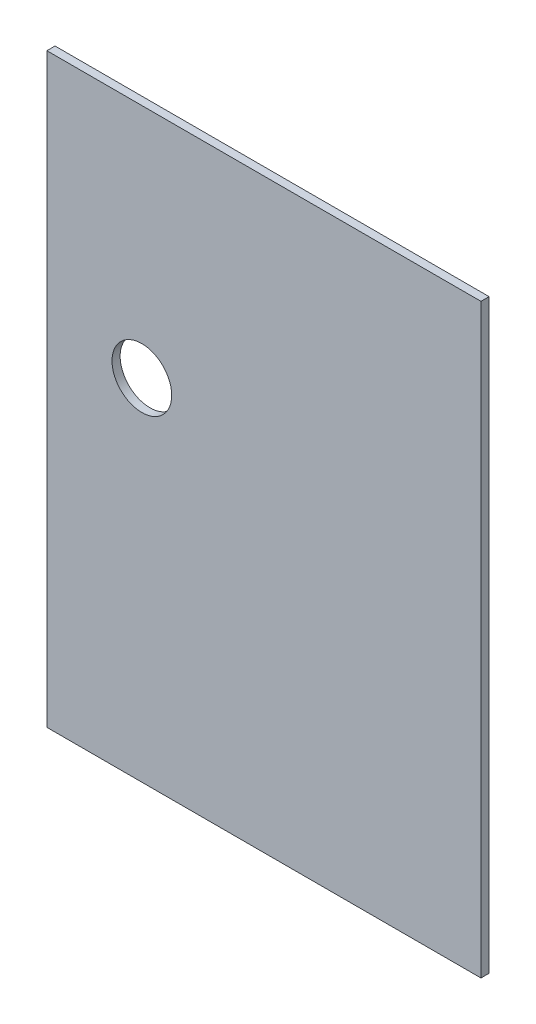
SolidWorks part; units mm, degrees
ref_plane "Front Plane" through (0, 0, 0) normal (0, 0, 1) x (1, 0, 0)
ref_plane "Top Plane" through (0, 0, 0) normal (0, 1, 0) x (1, 0, 0)
ref_plane "Right Plane" through (0, 0, 0) normal (1, 0, 0) x (0, 0, -1)
sketch "Sketch1" plane through (0, 0, 0) normal (0, 0, 1) x (1, 0, 0)
  line L1 (0, 0) -> (160, 0)
  line L2 (0, 0) -> (0, 216)
  line L3 (0, 216) -> (160, 216)
  line L4 (160, 0) -> (160, 216)
  dimension "D1" = 160
  dimension "D2" = 216
extrude "Boss-Extrude1" add sketch "Sketch1" along normal blind 3
sketch "Sketch2" plane through (0, 0, 3) normal (0, 0, 1) x (1, 0, 0)
  line L1 (0, 0) -> (160, 0) construction
  line L2 (0, 216) -> (0, 0) construction
  circle A0 centre (35, 129) radius 11
  dimension "D1" = 22
  dimension "D2" = 35
  dimension "D3" = 129
extrude "Cut-Extrude1" cut sketch "Sketch2" against normal blind 3
